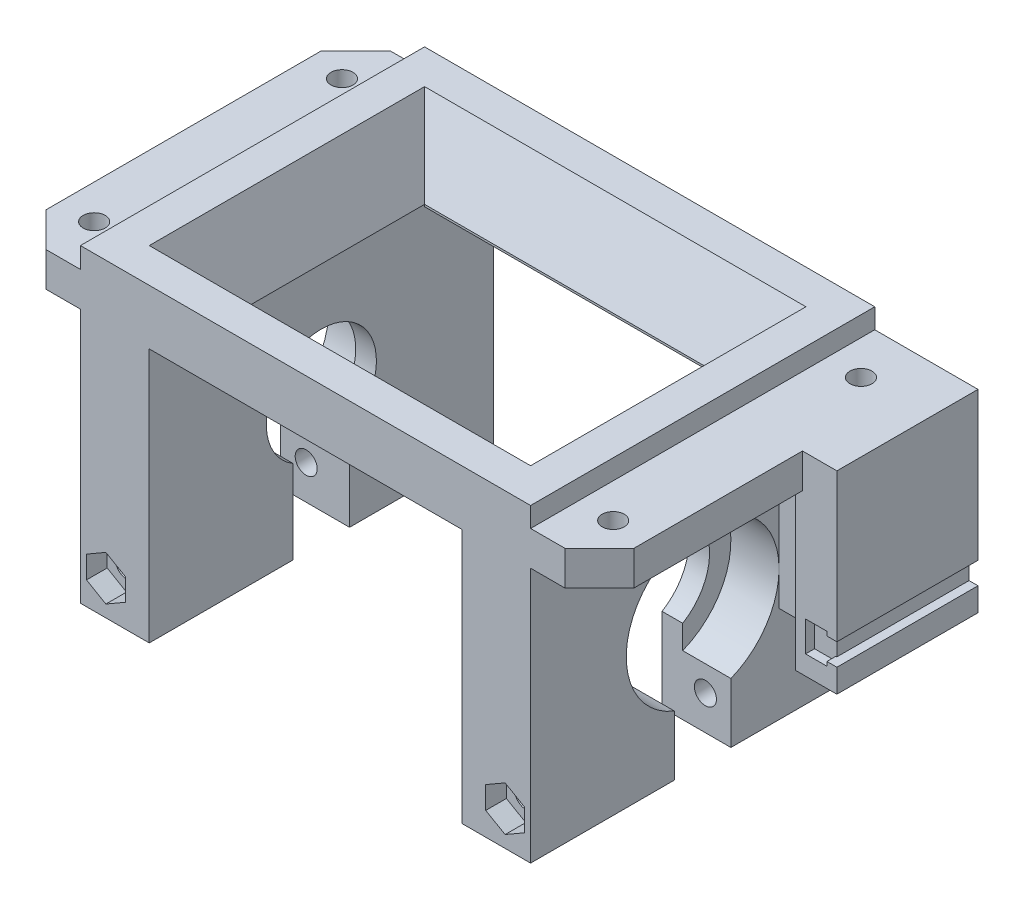
SolidWorks part; units mm, degrees
ref_plane "Спереди" through (0, 0, 0) normal (0, 0, 1) x (1, 0, 0)
ref_plane "Сверху" through (0, 0, 0) normal (0, 1, 0) x (1, 0, 0)
ref_plane "Справа" through (0, 0, 0) normal (1, 0, 0) x (0, 0, -1)
sketch "Sketch1" plane through (0, 0, 0) normal (0, 1, 0) x (1, 0, 0)
  line L1 (22.7, -15) -> (-22.7, -15)
  line L2 (22.7, -15) -> (22.7, 15)
  line L3 (22.7, 15) -> (-22.7, 15)
  line L4 (-22.7, -15) -> (-22.7, 15)
  line L5 (22.7, -15) -> (-22.7, 15) construction
  line L6 (22.7, 15) -> (-22.7, -15) construction
  line L7 (32.7, -30) -> (-32.7, -30)
  line L8 (32.7, -30) -> (32.7, 30)
  line L9 (32.7, 30) -> (-32.7, 30)
  line L10 (-32.7, -30) -> (-32.7, 30)
  line L11 (32.7, -30) -> (-32.7, 30) construction
  line L12 (32.7, 30) -> (-32.7, -30) construction
  point P0 (0, 0)
  point P6 (0, 0)
  dimension "D1" = 45.4
  dimension "D2" = 30
  dimension "D3" = 10
  dimension "D4" = 60
extrude "Boss-Extrude1" add sketch "Sketch1" along normal blind 40
sketch "Sketch2" plane through (32.7, 0, 0) normal (1, 0, 0) x (0, 0, -1)
  line L0 (0, 40) -> (0, 0) construction
  line L1 (-30, 40) -> (30, 40) construction
  line L2 (-30, 0) -> (30, 0) construction
  circle A0 centre (0, 24) radius 8
  dimension "D1" = 16
  dimension "D2" = 16
extrude "Cut-Extrude1" cut sketch "Sketch2" against normal through all
sketch "Sketch3" plane through (0, 0, 0) normal (0, -1, 0) x (1, 0, 0)
  line L0 (-32.7, 30) -> (32.7, 30) construction
  line L1 (22.7, -26) -> (-22.7, -26)
  line L2 (22.7, -26) -> (22.7, 26)
  line L3 (22.7, 26) -> (-22.7, 26)
  line L4 (-22.7, -26) -> (-22.7, 26)
  line L5 (22.7, -26) -> (-22.7, 26) construction
  line L6 (22.7, 26) -> (-22.7, -26) construction
  line L8 (22.7, 15) -> (22.7, -15) construction
  point P0 (0, 0)
  point P8 (22.7, 0)
  dimension "D1" = 4
extrude "Cut-Extrude2" cut sketch "Sketch3" against normal blind 37
chamfer "Chamfer1" distance 5 angle 30 1 edges at (0, 37, -15)
sketch "Sketch6" plane through (32.7, 0, 0) normal (1, 0, 0) x (0, 0, -1)
  line L0 (0, 40) -> (0, 0) construction
  line L1 (-30, 40) -> (30, 40) construction
  line L2 (-30, 0) -> (30, 0) construction
sketch "Sketch7" plane through (0, 40, 0) normal (0, 1, 0) x (1, 0, 0)
  line L0 (-32.7, -25) -> (32.7, -25) construction
  line L1 (-32.7, 30) -> (-32.7, -30) construction
  line L2 (32.7, -30) -> (32.7, 30) construction
  line L3 (0, -25) -> (0, -30) construction
  line L4 (-32.7, -30) -> (32.7, -30) construction
  line L7 (32.7, -30) -> (-32.7, -30)
  line L8 (32.7, -30) -> (32.7, -25)
  line L9 (32.7, -25) -> (-32.7, -25)
  line L10 (-32.7, -30) -> (-32.7, -25)
  line L11 (32.7, -30) -> (-32.7, -25) construction
  line L12 (32.7, -25) -> (-32.7, -30) construction
  point P10 (0, -27.5)
  dimension "D1" = 5
extrude "Cut-Extrude5" cut sketch "Sketch7" against normal through all
chamfer "Chamfer2" distance 3 angle 42 1 edges at (0, 37, 15)
sketch "Sketch8" plane through (0, 40, 0) normal (0, 1, 0) x (1, 0, 0)
  line L0 (-32.7, -25) -> (32.7, 30) construction
  line L1 (-22.7, 15) -> (22.7, -15) construction
  line L2 (32.7, -25) -> (-32.7, -25)
  line L3 (32.7, -25) -> (32.7, 30)
  line L4 (32.7, 30) -> (-32.7, 30)
  line L5 (-32.7, -25) -> (-32.7, 30)
  line L6 (32.7, -25) -> (-32.7, 30) construction
  line L7 (32.7, 30) -> (-32.7, -25) construction
  line L9 (22.7, 15) -> (-22.7, 15)
  line L10 (22.7, 15) -> (22.7, -15)
  line L11 (22.7, -15) -> (-22.7, -15)
  line L12 (-22.7, 15) -> (-22.7, -15)
  line L13 (22.7, 15) -> (-22.7, -15) construction
  line L14 (22.7, -15) -> (-22.7, 15) construction
  point P4 (0, 2.5)
  point P12 (0, 0)
extrude "Boss-Extrude2" add sketch "Sketch8" along normal blind 10
chamfer "Chamfer3" distance 5 angle 63 4 edges at (22.7, 50, 0) (0, 50, -15) (0, 50, 15) (-22.7, 50, 0)
sketch "Sketch10" plane through (32.7, 0, 0) normal (1, 0, 0) x (0, 0, -1)
  circle A0 centre (0, 24) radius 11.1
  dimension "D1" = 22.2
extrude "Cut-Extrude8" cut sketch "Sketch10" against normal blind 7
sketch "Sketch11" plane through (-32.7, 0, 0) normal (-1, 0, 0) x (0, 0, 1)
  circle A0 centre (0, 24) radius 11.1
  dimension "D1" = 22.2
extrude "Cut-Extrude9" cut sketch "Sketch11" against normal blind 7
sketch "Sketch12" plane through (0, 0, 0) normal (0, -1, 0) x (1, 0, 0)
  line L0 (32.7, 0) -> (-32.7, 0) construction
  line L2 (-32.7, -30) -> (-32.7, 25) construction
  line L3 (32.7, 25) -> (32.7, -30) construction
  line L4 (-32.7, -4.1) -> (32.7, -4.1)
  line L5 (-32.7, -4.1) -> (-32.7, 4.1)
  line L6 (-32.7, 4.1) -> (32.7, 4.1)
  line L7 (32.7, -4.1) -> (32.7, 4.1)
  line L8 (-32.7, -4.1) -> (32.7, 4.1) construction
  line L9 (-32.7, 4.1) -> (32.7, -4.1) construction
  point P5 (0, 0)
  dimension "D1" = 8.2
extrude "Cut-Extrude10" cut sketch "Sketch12" against normal blind 20
sketch "Sketch13" plane through (0, 50, 0) normal (0, 1, 0) x (1, 0, 0)
  line L0 (0, -20) -> (0, -25) construction
  line L1 (27.7, -20) -> (-27.7, -20) construction
  line L2 (-32.7, -25) -> (32.7, -25) construction
  line L3 (0, 20) -> (0, 25) construction
  line L4 (-27.7, 20) -> (27.7, 20) construction
  line L5 (32.7, 25) -> (-32.7, 25)
  line L6 (32.7, -25) -> (32.7, 30) construction
  line L7 (-32.7, 30) -> (-32.7, -25) construction
  line L8 (-32.7, 25) -> (-32.7, 30)
  line L9 (-32.7, 30) -> (32.7, 30)
  line L10 (32.7, 30) -> (32.7, 25)
  dimension "D1" = 5
extrude "Cut-Extrude11" cut sketch "Sketch13" against normal blind 3
chamfer "Chamfer4" distance 5 angle 45 2 edges at (-32.7, 23.5, -30) (32.7, 23.5, -30)
sketch "Sketch20" plane through (32.7, 0, 0) normal (1, 0, 0) x (0, 0, -1)
  line L0 (-25, 47.1071) -> (25, 47) construction
  line L1 (-25, 0) -> (-25, 50) construction
  line L2 (-25, 44.6071) -> (25, 44.6071) construction
  line L3 (25, 0) -> (25, 47) construction
  line L5 (25, 42.1071) -> (-25, 42.1071)
  line L6 (25, 42.1071) -> (25, 47.1071)
  line L7 (25, 47.1071) -> (-25, 47.1071)
  line L8 (-25, 42.1071) -> (-25, 47.1071)
  line L9 (25, 42.1071) -> (-25, 47.1071) construction
  line L10 (25, 47.1071) -> (-25, 42.1071) construction
  point P9 (0, 44.6071)
  dimension "D1" = 5
extrude "Boss-Extrude5" add sketch "Sketch20" along normal blind 10
sketch "Sketch21" plane through (-32.7, 0, 0) normal (-1, 0, 0) x (0, 0, 1)
  line L0 (-25, 47) -> (25, 47) construction
  line L1 (25, 0) -> (25, 50) construction
  line L2 (-25, 44.5) -> (25, 44.5) construction
  line L3 (-25, 47) -> (-25, 0) construction
  line L5 (25, 42) -> (-25, 42)
  line L6 (25, 42) -> (25, 47)
  line L7 (25, 47) -> (-25, 47)
  line L8 (-25, 42) -> (-25, 47)
  line L9 (25, 42) -> (-25, 47) construction
  line L10 (25, 47) -> (-25, 42) construction
  point P9 (0, 44.5)
  dimension "D1" = 5
extrude "Boss-Extrude6" add sketch "Sketch21" along normal blind 10
chamfer "Chamfer5" distance 5 angle 45 4 edges at (42.7, 44.6071, 25) (42.7, 44.6071, -25) (-42.7, 44.5, 25) (-42.7, 44.5, -25)
sketch "Sketch23" plane through (0, 47, 0) normal (0, 1, 0) x (1, 0, 0)
  line L0 (-37.7, 25) -> (-37.7, -25) construction
  line L1 (-37.7, 25) -> (-32.7, 25) construction
  line L2 (-37.7, -25) -> (-32.7, -25) construction
  circle A0 centre (-37.7, 18) radius 1.6
  circle A1 centre (-37.7, -18) radius 1.6
  point P10 (-37.7, 0)
  dimension "D1" = 3.2
  dimension "D2" = 36
  dimension "D3" = 18
  dimension "D4" = 5
extrude "Cut-Extrude15" cut sketch "Sketch23" against normal through all
sketch "Sketch24" plane through (32.7, 0, 0) normal (1, 0, 0) x (0, 0, -1)
  line L0 (11.1, 24) -> (25, 24) construction
  line L1 (25, 0) -> (25, 42.1071) construction
  line L3 (11.1, 19) -> (25, 19)
  line L4 (11.1, 19) -> (11.1, 29)
  line L5 (11.1, 29) -> (25, 29)
  line L6 (25, 19) -> (25, 29)
  line L7 (11.1, 19) -> (25, 29) construction
  line L8 (11.1, 29) -> (25, 19) construction
  arc A0 (4.1, 13.685) -> (-4.1, 13.685) centre (0, 24) ccw construction
  point P7 (18.05, 24)
  dimension "D1" = 10
extrude "Boss-Extrude7" add sketch "Sketch24" along normal blind 15
sketch "Sketch22" plane through (0, 47.1071, 0) normal (0, 1, 0) x (1, 0, 0)
  line L0 (37.7, -25) -> (37.7, 25) construction
  line L1 (37.7, -25) -> (32.7, -25) construction
  line L2 (37.7, 25) -> (32.7, 25) construction
  circle A0 centre (37.7, -18) radius 1.6
  circle A1 centre (37.7, 18) radius 1.6
  point P11 (37.7, 0)
  dimension "D2" = 3.2
  dimension "D1" = 5
  dimension "D3" = 36
  dimension "D4" = 18
extrude "Cut-Extrude14" cut sketch "Sketch22" against normal through all
sketch "Sketch25" plane through (0, 19, 0) normal (0, -1, 0) x (1, 0, 0)
  circle A0 centre (37.7, -18) radius 3.5
  dimension "D1" = 7
extrude "Cut-Extrude16" cut sketch "Sketch25" against normal up to surface (10 mm away) up to face at (37.7, 29, -19.6)
sketch "Sketch27" plane through (0, 0, -11.1) normal (0, 0, 1) x (1, 0, 0)
  line L0 (44.7, 29) -> (44.7, 19) construction
  line L1 (47.7, 29) -> (32.7, 29) construction
  line L2 (47.7, 19) -> (32.7, 19) construction
  line L4 (41.7, 19) -> (47.7, 19)
  line L5 (41.7, 19) -> (41.7, 29)
  line L6 (41.7, 29) -> (47.7, 29)
  line L7 (47.7, 19) -> (47.7, 29)
  line L8 (41.7, 19) -> (47.7, 29) construction
  line L9 (41.7, 29) -> (47.7, 19) construction
  point P6 (44.7, 24)
  dimension "D1" = 6
extrude "Boss-Extrude8" add sketch "Sketch27" along normal blind 6.6
sketch "Sketch28" plane through (0, 0, -4.5) normal (0, 0, 1) x (1, 0, 0)
  line L3 (46.25, 21.8) -> (46.25, 22.4)
  line L4 (46.25, 21.8) -> (43.15, 21.8)
  line L5 (46.25, 22.4) -> (47.7, 22.4)
  line L6 (46.25, 26.2) -> (43.15, 26.2)
  line L7 (43.15, 21.8) -> (43.15, 26.2)
  line L8 (46.25, 21.8) -> (43.15, 26.2) construction
  line L9 (46.25, 26.2) -> (43.15, 21.8) construction
  line L10 (47.7, 19) -> (47.7, 29) construction
  line L11 (47.7, 22.4) -> (47.7, 25.6)
  line L12 (47.7, 25.6) -> (46.25, 25.6)
  line L13 (46.25, 26.2) -> (46.25, 25.6)
  line L14 (41.7, 24) -> (47.7, 24) construction
  line L15 (41.7, 29) -> (41.7, 19) construction
  point P1 (44.7, 24)
  point P6 (44.7, 24)
  dimension "D1" = 3.1
  dimension "D2" = 4.4
  dimension "D3" = 3.2
extrude "Cut-Extrude18" cut sketch "Sketch28" against normal blind 1.3
sketch "Sketch29" plane through (47.7, 0, 0) normal (1, 0, 0) x (0, 0, -1)
  line L0 (5.8, 24) -> (25, 24) construction
  line L1 (5.8, 22.4) -> (5.8, 25.6) construction
  line L2 (25, 19) -> (25, 29) construction
  line L4 (25, 22.4) -> (5.8, 22.4)
  line L5 (25, 22.4) -> (25, 25.6)
  line L6 (25, 25.6) -> (5.8, 25.6)
  line L7 (5.8, 22.4) -> (5.8, 25.6)
  line L8 (25, 22.4) -> (5.8, 25.6) construction
  line L9 (25, 25.6) -> (5.8, 22.4) construction
  point P6 (15.4, 24)
extrude "Cut-Extrude19" cut sketch "Sketch29" against normal blind 1.3
sketch "Sketch30" plane through (0, 0, 25) normal (0, 0, 1) x (1, 0, 0)
  line L0 (-32.7, 10) -> (32.7, 10) construction
  line L1 (-32.7, 0) -> (-32.7, 42) construction
  line L2 (32.7, 0) -> (32.7, 42.1071) construction
  circle A0 centre (-29, 10) radius 1.6
  circle A1 centre (29, 10) radius 1.6
  point P10 (0, 10)
  dimension "D1" = 3.2
  dimension "D2" = 58
  dimension "D3" = 29
  dimension "D4" = 10
extrude "Cut-Extrude20" cut sketch "Sketch30" against normal through all
sketch "Sketch31" plane through (0, 0, 25) normal (0, 0, 1) x (1, 0, 0)
  line L1 (26.1854, 11.625) -> (26.1854, 8.375)
  line L2 (26.1854, 8.375) -> (29, 6.75)
  line L3 (29, 6.75) -> (31.8146, 8.375)
  line L4 (31.8146, 8.375) -> (31.8146, 11.625)
  line L5 (31.8146, 11.625) -> (29, 13.25)
  line L6 (29, 13.25) -> (26.1854, 11.625)
  line L7 (-31.8146, 11.625) -> (-31.8146, 8.375)
  line L8 (-31.8146, 8.375) -> (-29, 6.75)
  line L9 (-29, 6.75) -> (-26.1854, 8.375)
  line L10 (-26.1854, 8.375) -> (-26.1854, 11.625)
  line L11 (-26.1854, 11.625) -> (-29, 13.25)
  line L12 (-29, 13.25) -> (-31.8146, 11.625)
  line L15 (-32.7, 0) -> (-32.7, 42) construction
  line L16 (22.7, 37) -> (22.7, 0) construction
  circle A0 centre (29, 10) radius 3.25 construction
  circle A1 centre (-29, 10) radius 3.25 construction
  dimension "D1" = 6.5
extrude "Cut-Extrude21" cut sketch "Sketch31" against normal blind 3
sketch "Sketch32" plane through (0, 0, -30) normal (0, 0, -1) x (-1, 0, 0)
  circle A0 centre (-29, 10) radius 3.15
  circle A1 centre (29, 10) radius 3.15
  dimension "D1" = 6.3
extrude "Cut-Extrude22" cut sketch "Sketch32" against normal blind 5
sketch "Sketch33" plane through (0, 50, 0) normal (0, 1, 0) x (1, 0, 0)
  line L1 (-32.7, -25) -> (-32.7, 25) construction
  line L2 (-32.7, 25) -> (32.7, 25) construction
  line L3 (32.7, 25) -> (32.7, -25) construction
  line L4 (32.7, -25) -> (-32.7, -25) construction
  dimension "D1" = 65.4
  dimension "D2" = 50
sketch "Sketch35" plane through (0, 0, 0) normal (0, -1, 0) x (1, 0, 0)
  line L1 (-52.887, -50.9051) -> (52.887, -50.9051)
  line L2 (-52.887, -50.9051) -> (-52.887, 50.9051)
  line L3 (-52.887, 50.9051) -> (52.887, 50.9051)
  line L4 (52.887, -50.9051) -> (52.887, 50.9051)
  line L5 (-52.887, -50.9051) -> (52.887, 50.9051) construction
  line L6 (-52.887, 50.9051) -> (52.887, -50.9051) construction
  point P0 (0, 0)
extrude "Cut-Extrude23" cut sketch "Sketch35" against normal blind 5
chamfer "Chamfer6" distance 5 angle 45 1 edges at (0, 37, 25)
sketch "Sketch36" plane through (0, 47, 0) normal (0, 1, 0) x (1, 0, 0)
  line L0 (32.7, 25) -> (27.7, 30)
  line L1 (27.7, 30) -> (-27.7, 30)
  line L2 (-27.7, 30) -> (-32.7, 25)
  line L3 (-32.7, 25) -> (32.7, 25)
extrude "Cut-Extrude25" cut sketch "Sketch36" against normal through all
sketch "Sketch37" plane through (0, 29, 0) normal (0, 1, 0) x (1, 0, 0)
  line L0 (32.7, 11.1) -> (41.7, 11.1)
  line L1 (41.7, 11.1) -> (41.7, 4.5)
  line L2 (41.7, 4.5) -> (47.7, 4.5)
  line L3 (47.7, 4.5) -> (47.7, 25)
  line L4 (47.7, 25) -> (32.7, 25)
  line L5 (32.7, 25) -> (32.7, 11.1)
  circle A0 centre (37.7, 18) radius 3.5
extrude "Boss-Extrude9" add sketch "Sketch37" along normal up to surface (18.1071 mm away) up to face at (37.7, 47.1071, -16.4)
